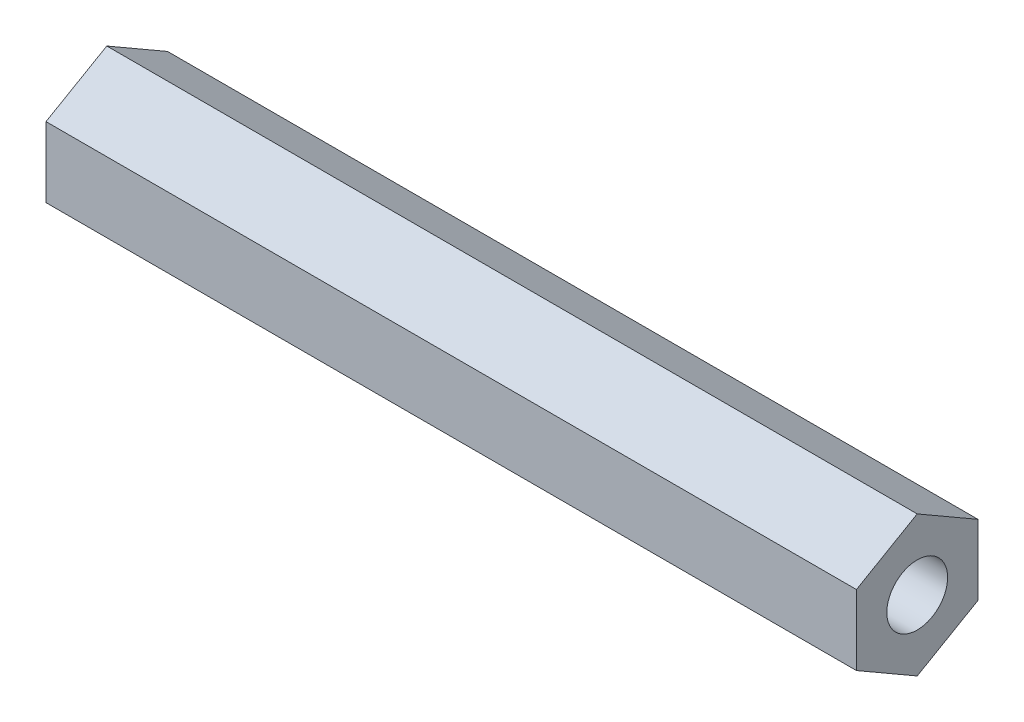
SolidWorks part; units mm, degrees
ref_plane "Front Plane" through (0, 0, 0) normal (0, 0, 1) x (1, 0, 0)
ref_plane "Top Plane" through (0, 0, 0) normal (0, 1, 0) x (1, 0, 0)
ref_plane "Right Plane" through (0, 0, 0) normal (1, 0, 0) x (0, 0, -1)
sketch "Sketch1" plane through (0, 0, 0) normal (1, 0, 0) x (0, 0, -1)
  line L7 (-42.7283, 8.2771) -> (-45.7283, 6.5451)
  line L8 (-45.7283, 6.5451) -> (-45.7283, 3.081)
  line L9 (-45.7283, 3.081) -> (-42.7283, 1.3489)
  line L10 (-42.7283, 1.3489) -> (-39.7283, 3.081)
  line L11 (-39.7283, 3.081) -> (-39.7283, 6.5451)
  line L12 (-39.7283, 6.5451) -> (-42.7283, 8.2771)
  circle A0 centre (-42.7283, 4.813) radius 1.5
  circle A2 centre (-42.7283, 4.813) radius 3 construction
  dimension "D1" = 3
extrude "Boss-Extrude1" add sketch "Sketch1" along normal blind 40
